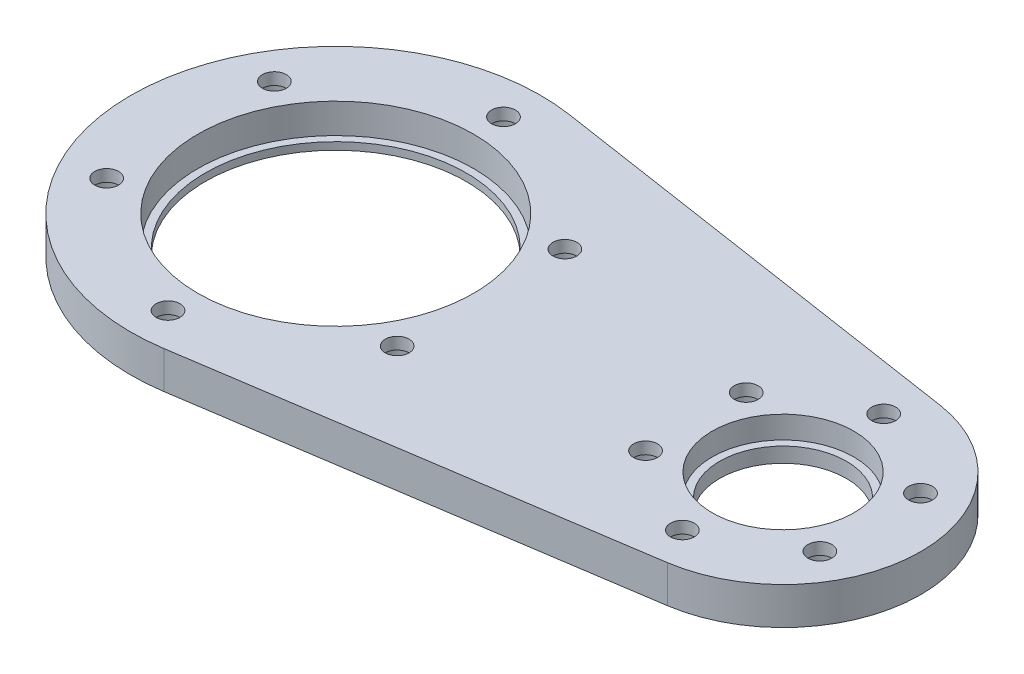
SolidWorks part; units mm, degrees
other "마크업1"
sketch "스케치8" plane through (80, 10, 22.5) normal (0.0741, 0.9433, 0.3234) x (0.9972, -0.0727, -0.0163)
sketch "스케치15" plane through (100, 13, 22.5) normal (0.0741, 0.9433, 0.3234) x (0.9972, -0.0727, -0.0163)
sketch "스케치16" plane through (100, 13, 22.5) normal (0.0741, 0.9433, 0.3234) x (0.9972, -0.0727, -0.0163)
sketch "스케치17" plane through (75, 13, 22.5) normal (0.0741, 0.9433, 0.3234) x (0.9972, -0.0727, -0.0163)
sketch "스케치23" plane through (75, 13, 22.5) normal (0.0741, 0.9433, 0.3234) x (0.9972, -0.0727, -0.0163)
sketch "스케치24" plane through (75, 10, 22.5) normal (0.0741, 0.9433, 0.3234) x (0.9972, -0.0727, -0.0163)
sketch "스케치25" plane through (75, 10, 25) normal (0.0741, 0.9433, 0.3234) x (0.9972, -0.0727, -0.0163)
sketch "스케치27" plane through (75, 5, 25) normal (0.0741, 0.9433, 0.3234) x (0.9972, -0.0727, -0.0163)
sketch "스케치29" plane through (75, 5, 25) normal (0.0741, 0.9433, 0.3234) x (0.9972, -0.0727, -0.0163)
sketch "스케치30" plane through (75, 4, 25) normal (0.0741, 0.9433, 0.3234) x (0.9972, -0.0727, -0.0163)
sketch "스케치37" plane through (78.5, 5, 27.5) normal (0.0741, 0.9433, 0.3234) x (0.9972, -0.0727, -0.0163)
material "7075-T6 (SN)"
ref_plane "정면" through (0, 0, 0) normal (0, 0, 1) x (1, 0, 0)
ref_plane "윗면" through (0, 0, 0) normal (0, 1, 0) x (1, 0, 0)
ref_plane "우측면" through (0, 0, 0) normal (1, 0, 0) x (0, 0, -1)
sketch "스케치1" plane through (0, 0, 0) normal (0, 1, 0) x (1, 0, 0)
  circle A0 centre (0, 0) radius 17.5
  circle A1 centre (0, 0) radius 27.5
  dimension "D1" = 35
  dimension "D2" = 55
extrude "보스-돌출1" add sketch "스케치1" along normal blind 4 contours A1 | A0
sketch "스케치2" plane through (0, 4, 0) normal (0, 1, 0) x (1, 0, 0)
  circle A0 centre (0, 0) radius 18.5
  circle A1 centre (0, 0) radius 27.5 construction
  circle A2 centre (0, 0) radius 27.5
  dimension "D1" = 37
extrude "보스-돌출2" add sketch "스케치2" along normal blind 5
sketch "스케치3" plane through (0, 9, 0) normal (0, 1, 0) x (1, 0, 0)
  line L0 (4.125, 27.1889) -> (62.775, 18.2907)
  line L1 (0, 0) -> (60, 0) construction
  line L2 (4.125, -27.1889) -> (62.775, -18.2907)
  circle A0 centre (0, 0) radius 27.5 construction
  arc A1 (4.125, -27.1889) -> (4.125, 27.1889) centre (0, 0) ccw
  arc A2 (62.775, -18.2907) -> (62.775, 18.2907) centre (60, 0) ccw
  dimension "D2" = 37
  dimension "D1" = 60
extrude "보스-돌출3" add sketch "스케치3" against normal blind 9
sketch "스케치7" plane through (0, 4, 0) normal (0, 1, 0) x (1, 0, 0)
  circle A0 centre (0, 0) radius 18.5 construction
  circle A1 centre (0, 0) radius 18.5
extrude "컷-돌출4" cut sketch "스케치7" against normal blind 3
sketch "스케치13" plane through (0, 0, 0) normal (0, -1, 0) x (1, 0, 0)
  circle A0 centre (60, 0) radius 9.5
  dimension "D1" = 19
extrude "컷-돌출9" cut sketch "스케치13" against normal blind 7
sketch "스케치14" plane through (0, 7, 0) normal (0, -1, 0) x (1, 0, 0)
  circle A0 centre (60, 0) radius 8.5
  dimension "D1" = 17
extrude "컷-돌출10" cut sketch "스케치14" against normal through all
sketch "스케치26" plane through (0, 0, 0) normal (1, 0, 0) x (0, 0, -1)
  line L0 (18.2907, 9) -> (-18.2907, 9) construction
  line L1 (-33.8225, 18.2258) -> (31.4643, 18.2258)
  line L2 (-33.8225, 18.2258) -> (-33.8225, 5)
  line L3 (-33.8225, 5) -> (31.4643, 5)
  line L4 (31.4643, 18.2258) -> (31.4643, 5)
  dimension "D1" = 4
extrude "컷-돌출11" cut sketch "스케치26" against normal mid plane 2222
sketch "스케치28" plane through (0, 0, 0) normal (0, -1, 0) x (1, 0, 0)
  circle A0 centre (60, 0) radius 8.5
  circle A1 centre (60, 0) radius 9.5
  circle A2 centre (60, 0) radius 9.5 construction
  dimension "D1" = 17
extrude "보스-돌출4" add sketch "스케치28" against normal blind 2
sketch "스케치31" plane through (0, 0, 0) normal (0, -1, 0) x (1, 0, 0)
  circle A0 centre (0, 0) radius 22.5 construction
  circle A1 centre (0, 0) radius 17.5 construction
  dimension "D1" = 45
hole_wizard "M3 육각 소켓 머리 캡 나사용 카운터보어1" positions "스케치32" profile "스케치33" counterbore size "M3" standard "ISO" end condition through all
sketch "스케치32" plane through (0, 0, 0) normal (0, -1, 0) x (-1, 0, 0)
  circle A0 centre (0, 0) radius 22.5 construction
  point P0 (0, 22.5)
sketch "스케치33" plane through (0, 0, -22.5) normal (1, 0, 0) x (0, 0, -1)
  line L0 (0, 0) -> (0, 5)
  line L1 (0, 5) -> (1.6, 5)
  line L3 (1.6, 5) -> (1.6, 3.4)
  line L4 (1.6, 3.4) -> (3.25, 3.4)
  line L5 (3.25, 3.4) -> (3.25, 0)
  line L7 (3.25, 0) -> (0, 0)
  line L11 (0, -6.35) -> (0, 107.95) construction
  dimension "관통 구멍 지름" = 3.2
  dimension "관통 구멍 깊이" = 5
  dimension "카운터보어 지름" = 6.5
  dimension "카운터보어 깊이" = 3.4
pattern_circular "원형 패턴1" count 6 over 360 about axis through (0, 0, 0) along (0, 1, 0) of "M3 육각 소켓 머리 캡 나사용 카운터보어1"
sketch "스케치34" plane through (0, 0, 0) normal (0, -1, 0) x (1, 0, 0)
  circle A0 centre (60, 0) radius 13.5 construction
  circle A1 centre (60, 0) radius 8.5 construction
  dimension "D1" = 27
hole_wizard "M3 육각 소켓 머리 캡 나사용 카운터보어2" positions "스케치35" profile "스케치36" counterbore size "M3" standard "ISO" end condition through all
sketch "스케치35" plane through (0, 0, 0) normal (0, -1, 0) x (-1, 0, 0)
  circle A0 centre (-60, 0) radius 13.5 construction
  point P0 (-60, 13.5)
sketch "스케치36" plane through (60, 0, -13.5) normal (1, 0, 0) x (0, 0, -1)
  line L0 (0, 0) -> (0, 5)
  line L1 (0, 5) -> (1.6, 5)
  line L3 (1.6, 5) -> (1.6, 3.4)
  line L4 (1.6, 3.4) -> (3.25, 3.4)
  line L5 (3.25, 3.4) -> (3.25, 0)
  line L7 (3.25, 0) -> (0, 0)
  line L11 (0, -6.35) -> (0, 107.95) construction
  dimension "관통 구멍 지름" = 3.2
  dimension "관통 구멍 깊이" = 5
  dimension "카운터보어 지름" = 6.5
  dimension "카운터보어 깊이" = 3.4
pattern_circular "원형 패턴2" count 6 over 360 about axis through (60, 0, 0) along (0, 1, 0) of "M3 육각 소켓 머리 캡 나사용 카운터보어2"
